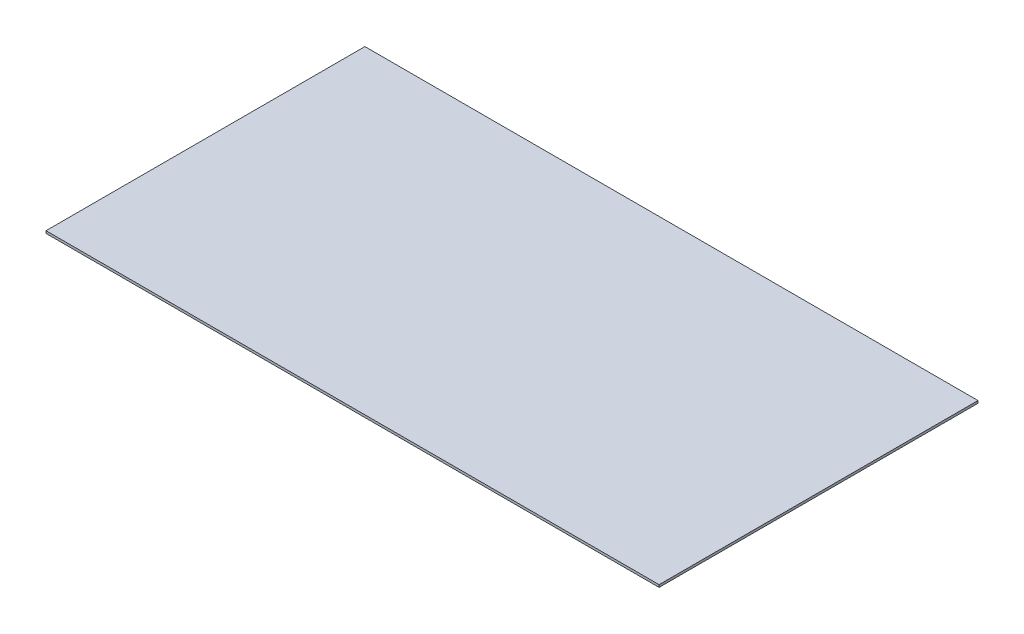
SolidWorks part; units mm, degrees
material "Silicon"
ref_plane "Front Plane" through (0, 0, 0) normal (0, 0, 1) x (1, 0, 0)
ref_plane "Top Plane" through (0, 0, 0) normal (0, 1, 0) x (1, 0, 0)
ref_plane "Right Plane" through (0, 0, 0) normal (1, 0, 0) x (0, 0, -1)
sketch "Sketch1" plane through (0, 0, 0) normal (0, 1, 0) x (1, 0, 0)
  line L1 (-38.45, 20) -> (38.45, 20)
  line L2 (-38.45, 20) -> (-38.45, -20)
  line L3 (-38.45, -20) -> (38.45, -20)
  line L4 (38.45, 20) -> (38.45, -20)
  line L5 (-38.45, 20) -> (38.45, -20) construction
  line L6 (-38.45, -20) -> (38.45, 20) construction
  point P0 (0, 0)
  dimension "D1" = 40
  dimension "D2" = 76.9
extrude "Extrude1" add sketch "Sketch1" along normal blind 0.3
